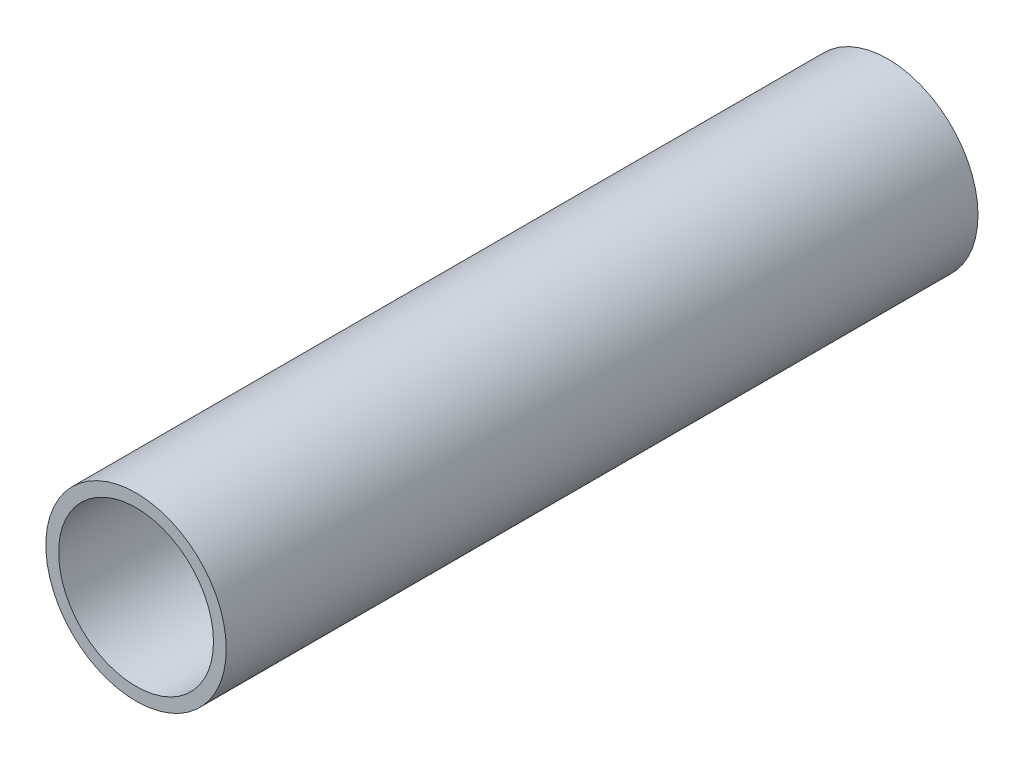
SolidWorks part; units mm, degrees
ref_plane "Front Plane" through (0, 0, 0) normal (0, 0, 1) x (1, 0, 0)
ref_plane "Top Plane" through (0, 0, 0) normal (0, 1, 0) x (1, 0, 0)
ref_plane "Right Plane" through (0, 0, 0) normal (1, 0, 0) x (0, 0, -1)
sketch "Sketch1" plane through (0, 0, 0) normal (0, 0, 1) x (1, 0, 0)
  circle A0 centre (0, 0) radius 24
  circle A1 centre (0, 0) radius 20.6
  dimension "D1" = 41.2
  dimension "D2" = 48
extrude "Boss-Extrude1" add sketch "Sketch1" against normal blind 200
